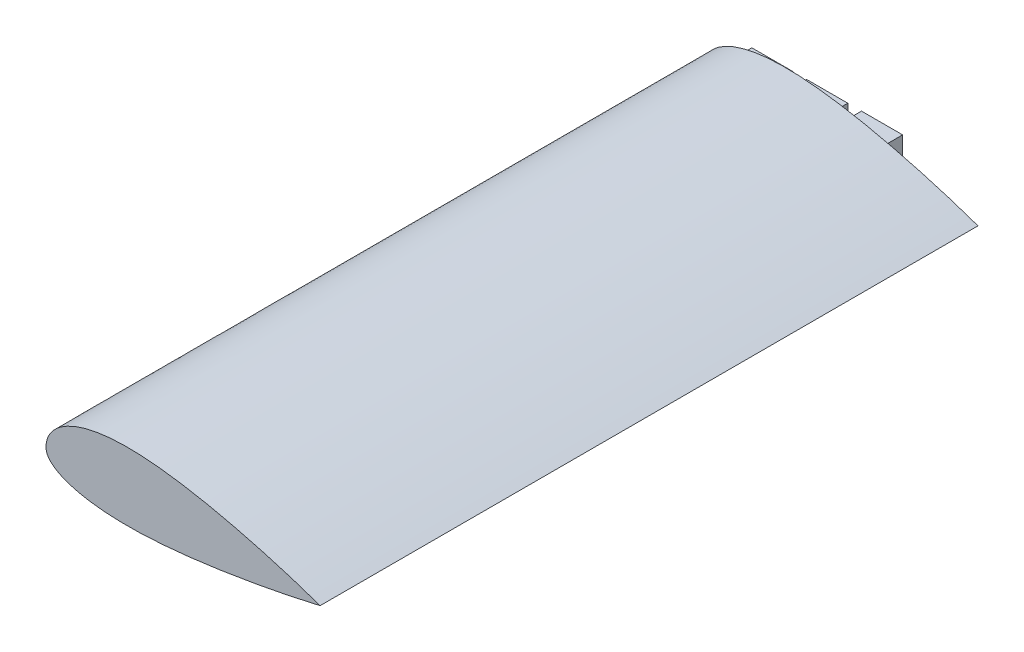
SolidWorks part; units mm, degrees
ref_plane "Front Plane" through (0, 0, 0) normal (0, 0, 1) x (1, 0, 0)
ref_plane "Top Plane" through (0, 0, 0) normal (0, 1, 0) x (1, 0, 0)
ref_plane "Right Plane" through (0, 0, 0) normal (1, 0, 0) x (0, 0, -1)
sketch "Sketch1" plane through (0, 0, 0) normal (0, 0, 1) x (1, 0, 0)
  spline S0 degree 4 poles (0, 0) (0.0009, 0.3297) (0.0295, 0.9275) (0.1439, 1.7967) (0.437, 2.9181) (0.8549, 3.9907) (1.4315, 5.0756) (2.1923, 6.1773) (3.2003, 7.33) (4.4959, 8.5106) (6.154, 9.7149) (8.2741, 10.9292) (10.957, 12.1146) (14.1477, 13.1525) (18.0405, 14.0363) (23.1343, 14.7366) (29.2357, 15.0274) (35.338, 14.8248) (41.1011, 14.3138) (46.841, 13.5968) (51.6037, 12.8505) (56.3456, 11.9834) (61.0671, 11.0139) (64.8328, 10.183) (68.5865, 9.3015) (72.3294, 8.3726) (76.0598, 7.3994) (79.3157, 6.5093) (82.096, 5.721) (84.4127, 5.0444) (86.2537, 4.4957) (88.1107, 3.9294) (89.9289, 3.3646) (91.806, 2.7666) (93.571, 2.1956) (95.5202, 1.5463) (97.1384, 1.0009) (99.1531, 0.3002) (100.3626, -0.127) (101.915, -0.6848) (103.1337, -1.1307) (104.3912, -1.5976) (105.6393, -2.0687) (106.8855, -2.5467) (108.1291, -3.0316) (109.0597, -3.4006) (109.6792, -3.6489) (109.9887, -3.7737) knots 0 0 0 0 0 0.011046 0.020082 0.029326 0.038802 0.04958 0.06121 0.074146 0.090071 0.108265 0.129827 0.155965 0.188307 0.220649 0.263591 0.328276 0.39296 0.425303 0.457645 0.522329 0.554672 0.587014 0.619356 0.651699 0.684041 0.716383 0.748725 0.764896 0.781068 0.797239 0.81341 0.829581 0.845752 0.861923 0.878094 0.894265 0.910437 0.921632 0.932827 0.944023 0.955218 0.966414 0.977609 0.988805 1 1 1 1 1 construction
  spline S1 degree 4 poles (0, 0) (0.0009, 0.3297) (0.0295, 0.9275) (0.1439, 1.7967) (0.437, 2.9181) (0.8549, 3.9907) (1.4315, 5.0756) (2.1923, 6.1773) (3.2003, 7.33) (4.4959, 8.5106) (6.154, 9.7149) (8.2741, 10.9292) (10.957, 12.1146) (14.1477, 13.1525) (18.0405, 14.0363) (23.1343, 14.7366) (29.2357, 15.0274) (35.338, 14.8248) (41.1011, 14.3138) (46.841, 13.5968) (51.6037, 12.8505) (56.3456, 11.9834) (61.0671, 11.0139) (64.8328, 10.183) (68.5865, 9.3015) (72.3294, 8.3726) (76.0598, 7.3994) (79.3157, 6.5093) (82.096, 5.721) (84.4127, 5.0444) (86.2537, 4.4957) (88.1107, 3.9294) (89.9289, 3.3646) (91.806, 2.7666) (93.571, 2.1956) (95.5202, 1.5463) (97.1383, 1.0009) (98.7751, 0.4317) (99.5867, 0.1465) (100.0002, 0) knots 0 0 0 0 0 0.011046 0.020082 0.029326 0.038802 0.04958 0.06121 0.074146 0.090071 0.108265 0.129827 0.155965 0.188307 0.220649 0.263591 0.328276 0.39296 0.425303 0.457645 0.522329 0.554672 0.587014 0.619356 0.651699 0.684041 0.716383 0.748725 0.764896 0.781068 0.797239 0.81341 0.829581 0.845752 0.861923 0.878094 0.894265 0.910434 0.910434 0.910434 0.910434 0.910434
  spline S2 degree 4 poles (0, 0) (0.0003, -0.1693) (0.016, -0.4614) (0.0775, -0.8851) (0.2333, -1.4356) (0.4512, -1.9609) (0.763, -2.5157) (1.1968, -3.1118) (1.8009, -3.7667) (2.6459, -4.4954) (3.845, -5.3152) (5.5202, -6.2106) (7.8905, -7.1807) (10.9471, -8.0963) (15.4296, -9.0396) (21.208, -9.73) (27.9775, -10.0275) (35.6486, -9.8891) (42.3469, -9.4657) (48.0748, -8.9399) (53.7915, -8.3061) (59.4968, -7.5766) (65.1885, -6.7461) (70.8667, -5.8302) (75.5899, -5.0142) (79.3624, -4.3307) (82.6596, -3.7058) (85.4801, -3.1515) (87.5962, -2.7233) (89.0005, -2.4341) (90.1811, -2.1872) (91.104, -1.9926) (92.3051, -1.7354) (93.6554, -1.4439) (95.3898, -1.0596) (97.1027, -0.6748) (99.4365, -0.1347) (101.1191, 0.2637) (103.9947, 0.9599) (105.7889, 1.4169) (107.9207, 1.9617) (109.0082, 2.2534) (109.6995, 2.4359) (109.9984, 2.5166) knots 0 0 0 0 0 0.005887 0.010193 0.014867 0.019889 0.025655 0.032315 0.040498 0.050865 0.064448 0.082823 0.106556 0.139954 0.175459 0.242256 0.309053 0.375849 0.442646 0.476045 0.509443 0.57624 0.643037 0.676435 0.709833 0.743232 0.77663 0.793329 0.810028 0.818378 0.826728 0.835077 0.843427 0.860126 0.876825 0.893524 0.910224 0.932668 0.955112 0.977556 0.988778 1 1 1 1 1 construction
  spline S3 degree 4 poles (0, 0) (0.0003, -0.1693) (0.016, -0.4614) (0.0775, -0.8851) (0.2333, -1.4356) (0.4512, -1.9609) (0.763, -2.5157) (1.1968, -3.1118) (1.8009, -3.7667) (2.6459, -4.4954) (3.845, -5.3152) (5.5202, -6.2106) (7.8905, -7.1807) (10.9471, -8.0963) (15.4296, -9.0396) (21.208, -9.73) (27.9775, -10.0275) (35.6486, -9.8891) (42.3469, -9.4657) (48.0748, -8.9399) (53.7915, -8.3061) (59.4968, -7.5766) (65.1885, -6.7461) (70.8667, -5.8302) (75.5899, -5.0142) (79.3624, -4.3307) (82.6596, -3.7058) (85.4801, -3.1515) (87.5962, -2.7233) (89.0005, -2.4341) (90.1811, -2.1872) (91.104, -1.9926) (92.3051, -1.7354) (93.6554, -1.4439) (95.3898, -1.0596) (97.1027, -0.6748) (98.7145, -0.3018) (99.5756, -0.1002) (100.0002, 0) knots 0 0 0 0 0 0.005887 0.010193 0.014867 0.019889 0.025655 0.032315 0.040498 0.050865 0.064448 0.082823 0.106556 0.139954 0.175459 0.242256 0.309053 0.375849 0.442646 0.476045 0.509443 0.57624 0.643037 0.676435 0.709833 0.743232 0.77663 0.793329 0.810028 0.818378 0.826728 0.835077 0.843427 0.860126 0.876825 0.893524 0.910224 0.910224 0.910224 0.910224 0.910224
sketch "Sketch2" plane through (0, 0, 0) normal (0, 1, 0) x (1, 0, 0)
  line L1 (0, 0) -> (0, -250) construction
  line L2 (0, -250) -> (50, -500) construction
  spline S0 degree 2 poles (0, 0) (0, -250) (50, -500) knots 0 0 0 1 1 1
  dimension "D1" = 250
  dimension "D2" = 250
  dimension "D3" = 50
ref_plane "Plane2" through (0, 0, 500) normal (0, 0, 1) x (1, 0, 0)
sketch "Sketch5" plane through (0, 0, 500) normal (0, 0, 1) x (1, 0, 0)
  spline S0 degree 4 poles (44.9961, 0) (44.997, 0.3297) (45.0257, 0.9275) (45.14, 1.7967) (45.4332, 2.9181) (45.851, 3.9907) (46.4276, 5.0756) (47.1884, 6.1773) (48.1965, 7.33) (49.4921, 8.5106) (51.1502, 9.7149) (53.2702, 10.9292) (55.9531, 12.1146) (59.1438, 13.1525) (63.0366, 14.0363) (68.1305, 14.7366) (74.2318, 15.0274) (80.3341, 14.8248) (86.0972, 14.3138) (91.8371, 13.5968) (96.5999, 12.8505) (101.3417, 11.9834) (106.0633, 11.0139) (109.8289, 10.183) (113.5826, 9.3015) (117.3256, 8.3726) (121.0559, 7.3994) (124.3119, 6.5093) (127.0921, 5.721) (129.4089, 5.0444) (131.2499, 4.4957) (133.1069, 3.9294) (134.9251, 3.3646) (136.8022, 2.7666) (138.5672, 2.1956) (140.5163, 1.5463) (142.1345, 1.0009) (144.1492, 0.3002) (145.3587, -0.127) (146.9111, -0.6848) (148.1299, -1.1307) (149.3874, -1.5976) (150.6354, -2.0687) (151.8817, -2.5467) (153.1253, -3.0316) (154.0559, -3.4006) (154.6753, -3.6489) (154.9848, -3.7737) knots 0 0 0 0 0 0.011046 0.020082 0.029326 0.038802 0.04958 0.06121 0.074146 0.090071 0.108265 0.129827 0.155965 0.188307 0.220649 0.263591 0.328276 0.39296 0.425303 0.457645 0.522329 0.554672 0.587014 0.619356 0.651699 0.684041 0.716383 0.748725 0.764896 0.781068 0.797239 0.81341 0.829581 0.845752 0.861923 0.878094 0.894265 0.910437 0.921632 0.932827 0.944023 0.955218 0.966414 0.977609 0.988805 1 1 1 1 1 construction
  spline S1 degree 4 poles (44.9961, 0) (44.997, 0.3297) (45.0257, 0.9275) (45.14, 1.7967) (45.4332, 2.9181) (45.851, 3.9907) (46.4276, 5.0756) (47.1884, 6.1773) (48.1965, 7.33) (49.4921, 8.5106) (51.1502, 9.7149) (53.2702, 10.9292) (55.9531, 12.1146) (59.1438, 13.1525) (63.0366, 14.0363) (68.1305, 14.7366) (74.2318, 15.0274) (80.3341, 14.8248) (86.0972, 14.3138) (91.8371, 13.5968) (96.5999, 12.8505) (101.3417, 11.9834) (106.0633, 11.0139) (109.8289, 10.183) (113.5826, 9.3015) (117.3256, 8.3726) (121.0559, 7.3994) (124.3119, 6.5093) (127.0921, 5.721) (129.4089, 5.0444) (131.2499, 4.4957) (133.1069, 3.9294) (134.9251, 3.3646) (136.8022, 2.7666) (138.5672, 2.1956) (140.5163, 1.5463) (142.1344, 1.0009) (143.7713, 0.4317) (144.5828, 0.1465) (144.9964, 0) knots 0 0 0 0 0 0.011046 0.020082 0.029326 0.038802 0.04958 0.06121 0.074146 0.090071 0.108265 0.129827 0.155965 0.188307 0.220649 0.263591 0.328276 0.39296 0.425303 0.457645 0.522329 0.554672 0.587014 0.619356 0.651699 0.684041 0.716383 0.748725 0.764896 0.781068 0.797239 0.81341 0.829581 0.845752 0.861923 0.878094 0.894265 0.910434 0.910434 0.910434 0.910434 0.910434 construction
  spline S2 degree 4 poles (44.9961, 0) (44.9964, -0.1693) (45.0121, -0.4614) (45.0736, -0.8851) (45.2294, -1.4356) (45.4474, -1.9609) (45.7592, -2.5157) (46.193, -3.1118) (46.7971, -3.7667) (47.642, -4.4954) (48.8411, -5.3152) (50.5163, -6.2106) (52.8866, -7.1807) (55.9432, -8.0963) (60.4257, -9.0396) (66.2041, -9.73) (72.9737, -10.0275) (80.6447, -9.8891) (87.343, -9.4657) (93.071, -8.9399) (98.7876, -8.3061) (104.493, -7.5766) (110.1846, -6.7461) (115.8628, -5.8302) (120.586, -5.0142) (124.3586, -4.3307) (127.6557, -3.7058) (130.4762, -3.1515) (132.5924, -2.7233) (133.9966, -2.4341) (135.1772, -2.1872) (136.1002, -1.9926) (137.3012, -1.7354) (138.6515, -1.4439) (140.3859, -1.0596) (142.0988, -0.6748) (144.4327, -0.1347) (146.1152, 0.2637) (148.9908, 0.9599) (150.7851, 1.4169) (152.9168, 1.9617) (154.0043, 2.2534) (154.6957, 2.4359) (154.9945, 2.5166) knots 0 0 0 0 0 0.005887 0.010193 0.014867 0.019889 0.025655 0.032315 0.040498 0.050865 0.064448 0.082823 0.106556 0.139954 0.175459 0.242256 0.309053 0.375849 0.442646 0.476045 0.509443 0.57624 0.643037 0.676435 0.709833 0.743232 0.77663 0.793329 0.810028 0.818378 0.826728 0.835077 0.843427 0.860126 0.876825 0.893524 0.910224 0.932668 0.955112 0.977556 0.988778 1 1 1 1 1 construction
  spline S3 degree 4 poles (44.9961, 0) (44.9964, -0.1693) (45.0121, -0.4614) (45.0736, -0.8851) (45.2294, -1.4356) (45.4474, -1.9609) (45.7592, -2.5157) (46.193, -3.1118) (46.7971, -3.7667) (47.642, -4.4954) (48.8411, -5.3152) (50.5163, -6.2106) (52.8866, -7.1807) (55.9432, -8.0963) (60.4257, -9.0396) (66.2041, -9.73) (72.9737, -10.0275) (80.6447, -9.8891) (87.343, -9.4657) (93.071, -8.9399) (98.7876, -8.3061) (104.493, -7.5766) (110.1846, -6.7461) (115.8628, -5.8302) (120.586, -5.0142) (124.3586, -4.3307) (127.6557, -3.7058) (130.4762, -3.1515) (132.5924, -2.7233) (133.9966, -2.4341) (135.1772, -2.1872) (136.1002, -1.9926) (137.3012, -1.7354) (138.6515, -1.4439) (140.3859, -1.0596) (142.0988, -0.6748) (143.7106, -0.3018) (144.5718, -0.1002) (144.9964, 0) knots 0 0 0 0 0 0.005887 0.010193 0.014867 0.019889 0.025655 0.032315 0.040498 0.050865 0.064448 0.082823 0.106556 0.139954 0.175459 0.242256 0.309053 0.375849 0.442646 0.476045 0.509443 0.57624 0.643037 0.676435 0.709833 0.743232 0.77663 0.793329 0.810028 0.818378 0.826728 0.835077 0.843427 0.860126 0.876825 0.893524 0.910224 0.910224 0.910224 0.910224 0.910224 construction
  spline S4 degree 1 poles (50, 0.1659) (125.4884, 0.9751) knots 0 0 1 1 construction
  spline S5 degree 1 poles (50, 0.1659) (125.4884, 0.9751) knots 0 0 1 1 construction
  spline S6 degree 3 poles (50, 0.1659) (50.0179, 0.6032) (50.1757, 1.4567) (50.8242, 2.7316) (51.9666, 4.0552) (54.0561, 5.71) (57.4359, 7.406) (62.0985, 8.7726) (67.0831, 9.581) (73.966, 10.0492) (82.8075, 9.7192) (93.5157, 8.3656) (107.7971, 5.6881) (118.4649, 2.9873) (125.4884, 0.9751) knots 0.003107 0.003107 0.003107 0.003107 0.026472 0.049837 0.073202 0.096568 0.143298 0.190028 0.236758 0.283489 0.376949 0.47041 0.56387 0.750791 0.750791 0.750791 0.750791
  spline S7 degree 3 poles (125.4884, 0.9751) (118.8048, -0.2943) (108.7202, -1.9955) (95.2701, -3.722) (85.1977, -4.6498) (76.8507, -4.9962) (70.2537, -4.8947) (65.3724, -4.5831) (61.4032, -4.0773) (58.338, -3.4825) (56.1227, -2.928) (54.0329, -2.2507) (52.4618, -1.576) (51.3904, -0.9852) (50.7151, -0.5321) (50.3053, -0.1828) (50.0857, 0.053) (50.0309, 0.1225) (50, 0.1659) knots 0.025551 0.025551 0.025551 0.025551 0.205368 0.295277 0.385186 0.475094 0.520049 0.565003 0.609957 0.632435 0.654912 0.677389 0.699866 0.711105 0.722343 0.733582 0.739201 0.74482 0.74482 0.74482 0.74482
  spline S8 degree 1 poles (57.6356, 1.8665) (100.2923, 1.9767) knots 0 0 1 1 construction
  spline S9 degree 1 poles (57.6356, 1.8665) (100.2923, 1.9767) knots 0 0 1 1 construction
  spline S10 degree 3 poles (57.6356, 1.8665) (57.9231, 2.0151) (58.4925, 2.2874) (59.782, 2.82) (61.5543, 3.4029) (63.8869, 3.9672) (67.1912, 4.5347) (71.5938, 4.9175) (77.127, 4.9346) (82.8116, 4.5908) (88.5912, 3.9528) (94.4204, 3.0772) (98.3432, 2.3598) (100.2923, 1.9767) knots 0.118651 0.118651 0.118651 0.118651 0.131754 0.144858 0.171065 0.197272 0.223479 0.275893 0.328307 0.380721 0.433135 0.485549 0.537964 0.537964 0.537964 0.537964
  spline S11 degree 3 poles (100.2923, 1.9767) (98.4159, 1.7345) (94.6502, 1.2813) (87.1702, 0.537) (79.7557, 0.0753) (72.5111, 0.0364) (68.0926, 0.2319) (64.6731, 0.551) (62.1863, 0.8819) (60.2071, 1.2401) (58.6967, 1.5822) (57.9917, 1.7662) (57.6356, 1.8665) knots 0.116889 0.116889 0.116889 0.116889 0.167972 0.219056 0.321223 0.372307 0.42339 0.448932 0.474474 0.500016 0.512787 0.525558 0.525558 0.525558 0.525558
  dimension "D1" = 5
  dimension "D3" = 50
  dimension "D2" = 10
sketch "Sketch6" plane through (0, 0, 0) normal (0, 0, 1) x (1, 0, 0)
  spline S0 degree 4 poles (0, 0) (0.0009, 0.3297) (0.0295, 0.9275) (0.1439, 1.7967) (0.437, 2.9181) (0.8549, 3.9907) (1.4315, 5.0756) (2.1923, 6.1773) (3.2003, 7.33) (4.4959, 8.5106) (6.154, 9.7149) (8.2741, 10.9292) (10.957, 12.1146) (14.1477, 13.1525) (18.0405, 14.0363) (23.1343, 14.7366) (29.2357, 15.0274) (35.338, 14.8248) (41.1011, 14.3138) (46.841, 13.5968) (51.6037, 12.8505) (56.3456, 11.9834) (61.0671, 11.0139) (64.8328, 10.183) (68.5865, 9.3015) (72.3294, 8.3726) (76.0598, 7.3994) (79.3157, 6.5093) (82.096, 5.721) (84.4127, 5.0444) (86.2537, 4.4957) (88.1107, 3.9294) (89.9289, 3.3646) (91.806, 2.7666) (93.571, 2.1956) (95.5202, 1.5463) (97.1384, 1.0009) (99.1531, 0.3002) (100.3626, -0.127) (101.915, -0.6848) (103.1337, -1.1307) (104.3912, -1.5976) (105.6393, -2.0687) (106.8855, -2.5467) (108.1291, -3.0316) (109.0597, -3.4006) (109.6792, -3.6489) (109.9887, -3.7737) knots 0 0 0 0 0 0.011046 0.020082 0.029326 0.038802 0.04958 0.06121 0.074146 0.090071 0.108265 0.129827 0.155965 0.188307 0.220649 0.263591 0.328276 0.39296 0.425303 0.457645 0.522329 0.554672 0.587014 0.619356 0.651699 0.684041 0.716383 0.748725 0.764896 0.781068 0.797239 0.81341 0.829581 0.845752 0.861923 0.878094 0.894265 0.910437 0.921632 0.932827 0.944023 0.955218 0.966414 0.977609 0.988805 1 1 1 1 1 construction
  spline S1 degree 4 poles (0, 0) (0.0009, 0.3297) (0.0295, 0.9275) (0.1439, 1.7967) (0.437, 2.9181) (0.8549, 3.9907) (1.4315, 5.0756) (2.1923, 6.1773) (3.2003, 7.33) (4.4959, 8.5106) (6.154, 9.7149) (8.2741, 10.9292) (10.957, 12.1146) (14.1477, 13.1525) (18.0405, 14.0363) (23.1343, 14.7366) (29.2357, 15.0274) (35.338, 14.8248) (41.1011, 14.3138) (46.841, 13.5968) (51.6037, 12.8505) (56.3456, 11.9834) (61.0671, 11.0139) (64.8328, 10.183) (68.5865, 9.3015) (72.3294, 8.3726) (76.0598, 7.3994) (79.3157, 6.5093) (82.096, 5.721) (84.4127, 5.0444) (86.2537, 4.4957) (88.1107, 3.9294) (89.9289, 3.3646) (91.806, 2.7666) (93.571, 2.1956) (95.5202, 1.5463) (97.1383, 1.0009) (98.7751, 0.4317) (99.5867, 0.1465) (100.0002, 0) knots 0 0 0 0 0 0.011046 0.020082 0.029326 0.038802 0.04958 0.06121 0.074146 0.090071 0.108265 0.129827 0.155965 0.188307 0.220649 0.263591 0.328276 0.39296 0.425303 0.457645 0.522329 0.554672 0.587014 0.619356 0.651699 0.684041 0.716383 0.748725 0.764896 0.781068 0.797239 0.81341 0.829581 0.845752 0.861923 0.878094 0.894265 0.910434 0.910434 0.910434 0.910434 0.910434 construction
  spline S2 degree 4 poles (0, 0) (0.0003, -0.1693) (0.016, -0.4614) (0.0775, -0.8851) (0.2333, -1.4356) (0.4512, -1.9609) (0.763, -2.5157) (1.1968, -3.1118) (1.8009, -3.7667) (2.6459, -4.4954) (3.845, -5.3152) (5.5202, -6.2106) (7.8905, -7.1807) (10.9471, -8.0963) (15.4296, -9.0396) (21.208, -9.73) (27.9775, -10.0275) (35.6486, -9.8891) (42.3469, -9.4657) (48.0748, -8.9399) (53.7915, -8.3061) (59.4968, -7.5766) (65.1885, -6.7461) (70.8667, -5.8302) (75.5899, -5.0142) (79.3624, -4.3307) (82.6596, -3.7058) (85.4801, -3.1515) (87.5962, -2.7233) (89.0005, -2.4341) (90.1811, -2.1872) (91.104, -1.9926) (92.3051, -1.7354) (93.6554, -1.4439) (95.3898, -1.0596) (97.1027, -0.6748) (99.4365, -0.1347) (101.1191, 0.2637) (103.9947, 0.9599) (105.7889, 1.4169) (107.9207, 1.9617) (109.0082, 2.2534) (109.6995, 2.4359) (109.9984, 2.5166) knots 0 0 0 0 0 0.005887 0.010193 0.014867 0.019889 0.025655 0.032315 0.040498 0.050865 0.064448 0.082823 0.106556 0.139954 0.175459 0.242256 0.309053 0.375849 0.442646 0.476045 0.509443 0.57624 0.643037 0.676435 0.709833 0.743232 0.77663 0.793329 0.810028 0.818378 0.826728 0.835077 0.843427 0.860126 0.876825 0.893524 0.910224 0.932668 0.955112 0.977556 0.988778 1 1 1 1 1 construction
  spline S3 degree 4 poles (0, 0) (0.0003, -0.1693) (0.016, -0.4614) (0.0775, -0.8851) (0.2333, -1.4356) (0.4512, -1.9609) (0.763, -2.5157) (1.1968, -3.1118) (1.8009, -3.7667) (2.6459, -4.4954) (3.845, -5.3152) (5.5202, -6.2106) (7.8905, -7.1807) (10.9471, -8.0963) (15.4296, -9.0396) (21.208, -9.73) (27.9775, -10.0275) (35.6486, -9.8891) (42.3469, -9.4657) (48.0748, -8.9399) (53.7915, -8.3061) (59.4968, -7.5766) (65.1885, -6.7461) (70.8667, -5.8302) (75.5899, -5.0142) (79.3624, -4.3307) (82.6596, -3.7058) (85.4801, -3.1515) (87.5962, -2.7233) (89.0005, -2.4341) (90.1811, -2.1872) (91.104, -1.9926) (92.3051, -1.7354) (93.6554, -1.4439) (95.3898, -1.0596) (97.1027, -0.6748) (98.7145, -0.3018) (99.5756, -0.1002) (100.0002, 0) knots 0 0 0 0 0 0.005887 0.010193 0.014867 0.019889 0.025655 0.032315 0.040498 0.050865 0.064448 0.082823 0.106556 0.139954 0.175459 0.242256 0.309053 0.375849 0.442646 0.476045 0.509443 0.57624 0.643037 0.676435 0.709833 0.743232 0.77663 0.793329 0.810028 0.818378 0.826728 0.835077 0.843427 0.860126 0.876825 0.893524 0.910224 0.910224 0.910224 0.910224 0.910224 construction
  spline S4 degree 1 poles (5.0039, 0.1659) (80.4922, 0.9751) knots 0 0 1 1 construction
  spline S5 degree 1 poles (5.0039, 0.1659) (80.4922, 0.9751) knots 0 0 1 1 construction
  spline S6 degree 3 poles (5.0039, 0.1659) (5.0218, 0.6032) (5.1796, 1.4567) (5.8281, 2.7316) (6.9704, 4.0552) (9.0599, 5.71) (12.4398, 7.406) (17.1024, 8.7726) (22.0869, 9.581) (28.9699, 10.0492) (37.8114, 9.7192) (48.5196, 8.3656) (62.801, 5.6881) (73.4687, 2.9873) (80.4922, 0.9751) knots 0.003107 0.003107 0.003107 0.003107 0.026472 0.049837 0.073202 0.096568 0.143298 0.190028 0.236758 0.283489 0.376949 0.47041 0.56387 0.750791 0.750791 0.750791 0.750791
  spline S7 degree 3 poles (80.4922, 0.9751) (73.8087, -0.2943) (63.7241, -1.9955) (50.274, -3.722) (40.2016, -4.6498) (31.8546, -4.9962) (25.2576, -4.8947) (20.3763, -4.5831) (16.407, -4.0773) (13.3418, -3.4825) (11.1266, -2.928) (9.0368, -2.2507) (7.4657, -1.576) (6.3942, -0.9852) (5.719, -0.5321) (5.3091, -0.1828) (5.0896, 0.053) (5.0347, 0.1225) (5.0039, 0.1659) knots 0.025551 0.025551 0.025551 0.025551 0.205368 0.295277 0.385186 0.475094 0.520049 0.565003 0.609957 0.632435 0.654912 0.677389 0.699866 0.711105 0.722343 0.733582 0.739201 0.74482 0.74482 0.74482 0.74482
  dimension "D1" = 5
extrude "Boss-Extrude1" add sketch "Sketch1" along normal mid plane 250
extrude "Cut-Extrude1" cut sketch "Sketch6" against normal blind 110 and the other way blind 120
sketch "Sketch7" plane through (0, 0, -125) normal (0, 0, -1) x (-1, 0, 0)
  line L1 (-22.5, -5) -> (-7.5, -5)
  line L2 (-22.5, -5) -> (-22.5, 5)
  line L3 (-22.5, 5) -> (-7.5, 5)
  line L4 (-7.5, -5) -> (-7.5, 5)
  line L5 (-27.5, 5) -> (-42.5, 5)
  line L6 (-27.5, 5) -> (-27.5, -5)
  line L7 (-27.5, -5) -> (-42.5, -5)
  line L8 (-42.5, 5) -> (-42.5, -5)
  line L9 (-47.5, 5) -> (-62.5, 5)
  line L10 (-47.5, 5) -> (-47.5, -5)
  line L11 (-47.5, -5) -> (-62.5, -5)
  line L12 (-62.5, 5) -> (-62.5, -5)
  point P5 (-7.5, 0)
  point P12 (-27.5, 0)
  point P14 (-35, 5)
  point P19 (-47.5, 0)
  dimension "D1" = 35
  dimension "D2" = 15
  dimension "D3" = 10
  dimension "D4" = 15
  dimension "D5" = 10
  dimension "D6" = 5
  dimension "D7" = 10
  dimension "D8" = 15
  dimension "D9" = 5
extrude "Cut-Extrude2" cut sketch "Sketch7" against normal blind 10 flip side to cut
